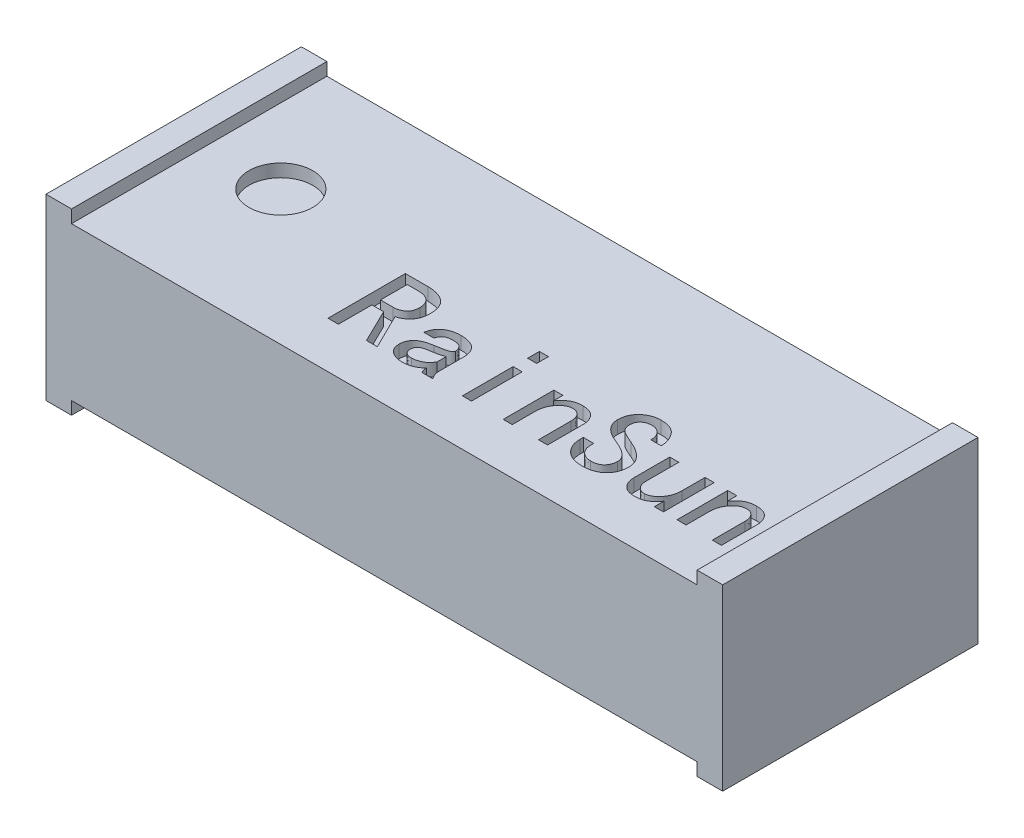
SolidWorks part; units mm, degrees
ref_plane "前视基准面" through (0, 0, 0) normal (0, 0, 1) x (1, 0, 0)
ref_plane "上视基准面" through (0, 0, 0) normal (0, 1, 0) x (1, 0, 0)
ref_plane "右视基准面" through (0, 0, 0) normal (1, 0, 0) x (0, 0, -1)
sketch "草图1" plane through (0, 0, 0) normal (0, 1, 0) x (1, 0, 0)
  line L1 (0, 0) -> (5.1, 0)
  line L2 (0, 0) -> (0, 2)
  line L3 (0, 2) -> (5.1, 2)
  line L4 (5.1, 0) -> (5.1, 2)
  dimension "D1" = 5.1
  dimension "D2" = 2
extrude "凸台-拉伸1" add sketch "草图1" along normal blind 1.2
sketch "草图2" plane through (0, 0, 0) normal (0, 0, 1) x (1, 0, 0)
  line L0 (0, 1.2) -> (0.1, 1.2)
  line L1 (0, 1.2) -> (5.1, 1.2) construction
  line L2 (0.1, 1.2) -> (0.1, 1.3)
  line L3 (0.1, 1.3) -> (-0.1, 1.3)
  line L4 (-0.1, 1.3) -> (-0.1, -0.1)
  line L5 (-0.1, -0.1) -> (0.1, -0.1)
  line L6 (0.1, -0.1) -> (0.1, 0)
  line L7 (0, 0) -> (5.1, 0) construction
  line L8 (0.1, 0) -> (0, 0)
  line L9 (0, 0) -> (0, 1.2)
  line L10 (2.55, 1.2) -> (2.55, 0) construction
  line L11 (5.1, 0) -> (5.1, 1.2)
  line L12 (5, 0) -> (5.1, 0)
  line L13 (5, -0.1) -> (5, 0)
  line L14 (5.2, -0.1) -> (5, -0.1)
  line L15 (5.2, 1.3) -> (5.2, -0.1)
  line L16 (5, 1.3) -> (5.2, 1.3)
  line L17 (5, 1.2) -> (5, 1.3)
  line L18 (5.1, 1.2) -> (5, 1.2)
  dimension "D1" = 0.1
  dimension "D2" = 0.1
  dimension "D3" = 0.2
  dimension "D4" = 0.1
  dimension "D5" = 0.1
extrude "凸台-拉伸2" add sketch "草图2" against normal blind 2
sketch "草图3" plane through (0, 1.2, 0) normal (0, 1, 0) x (1, 0, 0)
  line L0 (1.7068, 0.3452) -> (5, 0.3452) construction
  line L1 (5, 2) -> (5, 0) construction
  text T0 "RainSun" font "黑体" height in points 2
  point P5 (1.1378, 0.3516)
  point P6 (1.8297, 0.3516)
  point P7 (1.4223, 0.3516)
  point P8 (1.8943, 0.3452)
  point P9 (1.7068, 0.3452)
extrude "切除-拉伸1" cut sketch "草图3" against normal blind 0.1
sketch "草图4" plane through (0, 1.2, 0) normal (0, 1, 0) x (1, 0, 0)
  circle A0 centre (0.6848, 1.0545) radius 0.25
  dimension "D1" = 0.5
extrude "切除-拉伸2" cut sketch "草图4" against normal blind 0.1
